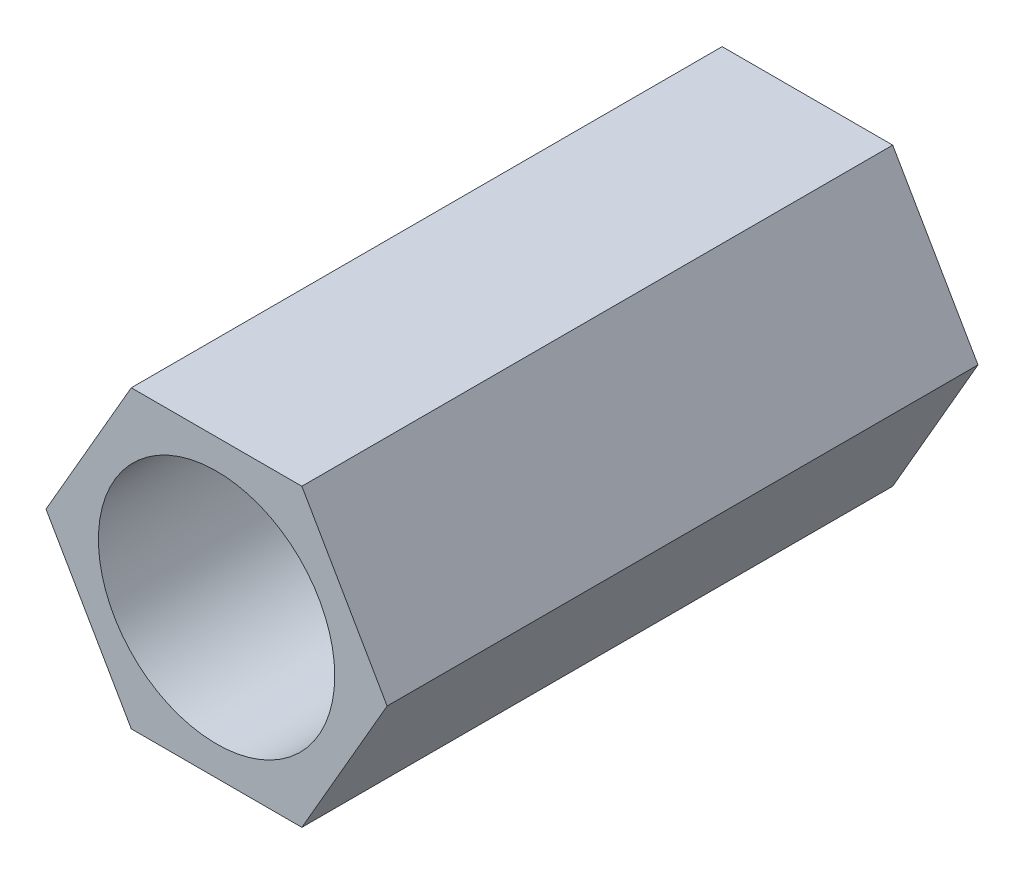
SolidWorks part; units mm, degrees
ref_plane "前视基准面" through (0, 0, 0) normal (0, 0, 1) x (1, 0, 0)
ref_plane "上视基准面" through (0, 0, 0) normal (0, 1, 0) x (1, 0, 0)
ref_plane "右视基准面" through (0, 0, 0) normal (1, 0, 0) x (0, 0, -1)
sketch "草图1" plane through (0, 0, 0) normal (0, 0, 1) x (1, 0, 0)
  line L1 (5.7735, 0) -> (2.8868, 5)
  line L2 (2.8868, 5) -> (-2.8868, 5)
  line L3 (-2.8868, 5) -> (-5.7735, 0)
  line L4 (-5.7735, 0) -> (-2.8868, -5)
  line L5 (-2.8868, -5) -> (2.8868, -5)
  line L6 (2.8868, -5) -> (5.7735, 0)
  circle A0 centre (0, 0) radius 5 construction
  dimension "D1" = 10
extrude "凸台-拉伸1" add sketch "草图1" along normal blind 20
sketch "草图2" plane through (0, 0, 20) normal (0, 0, 1) x (1, 0, 0)
  circle A0 centre (0, 0) radius 4
  dimension "D1" = 8
extrude "切除-拉伸1" cut sketch "草图2" against normal blind 20
